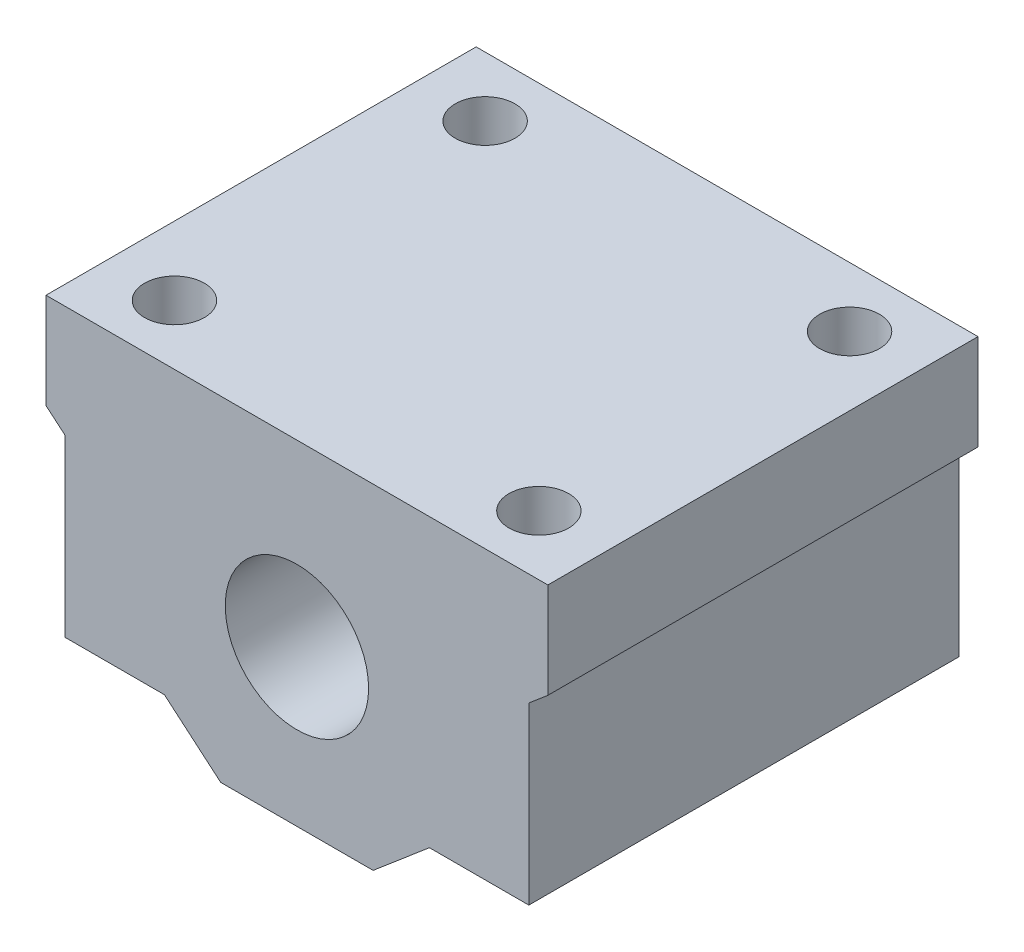
SolidWorks part; units mm, degrees
ref_plane "Plano frontal" through (0, 0, 0) normal (0, 0, 1) x (1, 0, 0)
ref_plane "Plano superior" through (0, 0, 0) normal (0, 1, 0) x (1, 0, 0)
ref_plane "Plano direito" through (0, 0, 0) normal (1, 0, 0) x (0, 0, -1)
sketch "Esboço1" plane through (0, 0, 0) normal (0, 0, 1) x (1, 0, 0)
  line L0 (0, -21.3481) -> (0, 26.1921) construction
  line L1 (6.3778, -6.0121) -> (-6.3778, -6.0121)
  line L2 (-6.3778, -6.0121) -> (-11.0891, -2.0121)
  line L3 (-11.0891, -2.0121) -> (-19.4109, -2.0121)
  line L4 (-19.4109, -2.0121) -> (-19.4109, 12.6387)
  line L5 (-19.4109, 12.6387) -> (-21, 13.9879)
  line L6 (-21, 13.9879) -> (-21, 21.9879)
  line L7 (-21, 21.9879) -> (21, 21.9879)
  line L8 (21, 13.9879) -> (21, 21.9879)
  line L9 (19.4109, 12.6387) -> (21, 13.9879)
  line L10 (19.4109, -2.0121) -> (19.4109, 12.6387)
  line L11 (11.0891, -2.0121) -> (19.4109, -2.0121)
  line L12 (6.3778, -6.0121) -> (11.0891, -2.0121)
  point P5 (-15.25, -2.0121)
  point P13 (0, 21.9879)
  point P18 (0, -6.0121)
  dimension "D1" = 21
  dimension "D2" = 24
  dimension "D3" = 8
  dimension "D4" = 28
  dimension "D5" = 15.25
extrude "Ressalto-extrusão1" add sketch "Esboço1" along normal blind 36
sketch "Esboço2" plane through (0, 0, 36) normal (0, 0, 1) x (1, 0, 0)
  line L0 (0, -8.0638) -> (0, 23.358) construction
  line L1 (21, 21.9879) -> (-21, 21.9879) construction
  circle A0 centre (0, 6.9879) radius 6
  dimension "D2" = 12
  dimension "D1" = 15
extrude "Corte-extrusão1" cut sketch "Esboço2" against normal through all
sketch "Esboço4" plane through (0, -6.0121, 0) normal (0, -1, 0) x (1, 0, 0)
  line L0 (0, -4.8411) -> (0, 38.5338) construction
  line L1 (19.4109, 18) -> (-21, 18) construction
  line L2 (-19.4109, 0) -> (-11.0891, 0) construction
  line L3 (-21, 36) -> (-21, 0) construction
  line L4 (19.4109, 36) -> (19.4109, 0) construction
  circle A0 centre (-15.25, 5) radius 2.5
  circle A4 centre (-15.25, 31) radius 2.5
  circle A5 centre (15.25, 5) radius 2.5
  circle A6 centre (15.25, 31) radius 2.5
  dimension "D1" = 5
  dimension "D2" = 5
  dimension "D3" = 5.75
extrude "Corte-extrusão2" cut sketch "Esboço4" against normal through all
